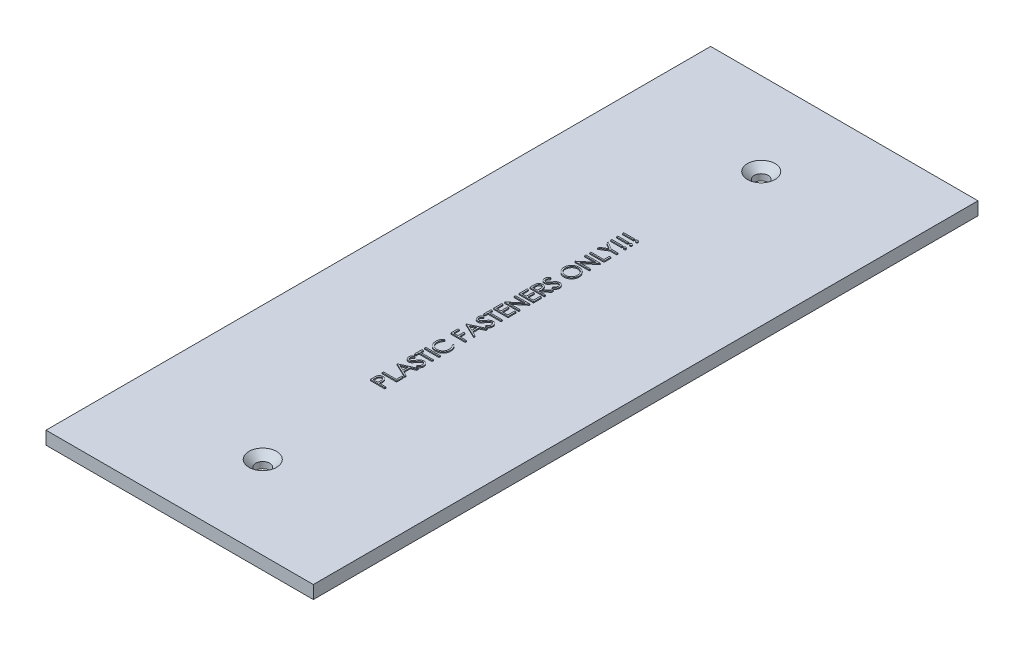
SolidWorks part; units mm, degrees
material "ABS"
ref_plane "Front Plane" through (0, 0, 0) normal (0, 0, 1) x (1, 0, 0)
ref_plane "Top Plane" through (0, 0, 0) normal (0, 1, 0) x (1, 0, 0)
ref_plane "Right Plane" through (0, 0, 0) normal (1, 0, 0) x (0, 0, -1)
sketch "Sketch1" plane through (0, 0, 0) normal (0, 1, 0) x (1, 0, 0)
  line L1 (0, 0) -> (65, 0)
  line L2 (0, 0) -> (0, 161.6)
  line L3 (0, 161.6) -> (65, 161.6)
  line L4 (65, 0) -> (65, 161.6)
  dimension "D1" = 65
  dimension "D2" = 161.6
extrude "Boss-Extrude1" add sketch "Sketch1" along normal blind 3.175
hole_wizard "CSK for M3 SFHCS1" positions "Sketch3" profile "Sketch2" countersink size "M3" standard "ANSI Metric" end condition through all
sketch "Sketch3" plane through (0, 3.175, 0) normal (0, 1, 0) x (1, 0, 0)
  line L4 (32.5, 0) -> (32.5, 161.6) construction
  line L5 (0, 0) -> (65, 0) construction
  line L6 (65, 161.6) -> (0, 161.6) construction
  point P17 (32.5, 20.2)
  point P19 (32.5, 141.4)
  dimension "D1" = 20.2
  dimension "D2" = 20.2
sketch "Sketch2" plane through (32.5, 3.175, -20.2) normal (1, 0, 0) x (0, 0, 1)
  line L0 (0, 0) -> (0, 3.175)
  line L1 (0, 3.175) -> (1.7, 3.175)
  line L2 (1.7, 3.175) -> (1.7, 1.66)
  line L3 (1.7, 1.66) -> (3.36, 0)
  line L5 (3.36, 0) -> (0, 0)
  line L6 (-1.7, 1.66) -> (-3.36, 0) construction
  line L11 (0, -6.35) -> (0, 107.95) construction
  dimension "Thru Hole Dia." = 3.4
  dimension "Thru Hole Depth" = 3.175
  dimension "Near C'Sink Dia." = 6.72
  dimension "Near C'Sink Angle" = 90
sketch "Sketch4" plane through (0, 3.175, 0) normal (0, 1, 0) x (1, 0, 0)
  line L0 (32.5, 20.2) -> (32.5, 141.4) construction
  text T0 "PLASTIC FASTENERS ONLY!!!"
extrude "Boss-Extrude2" add sketch "Sketch4" along normal blind 0.25
equation "\"ABS_thickness\" = 1.59\t"
equation "\"Bus_bar_thickness\" = 3.175"
equation "\"Connector_width\" = 20.2"
equation "\"Number_of_cells_long\" = 25"
equation "\"Number_of_cells_wide\" = 2"
equation "\"Cell_height\" = 65.0"
equation "\"Cell_diam\" = 18.0"
equation "\"D1@Boss-Extrude1\"=\"Bus_bar_thickness\""
equation "\"D1@Sketch3\"=\"Connector_width\""
equation "\"D2@Sketch3\"=\"Connector_width\""
equation "\"D2@Sketch1\"=\"Connector_width\"*8"
